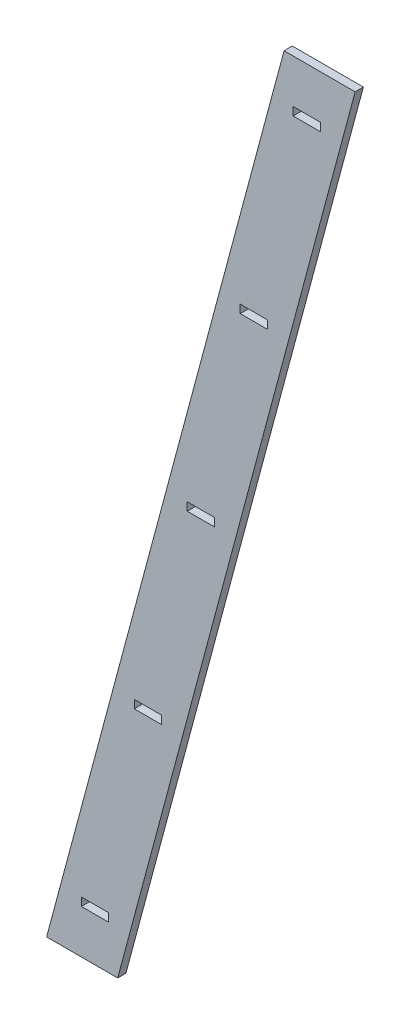
SolidWorks part; units mm, degrees
ref_plane "Alzado" through (0, 0, 0) normal (0, 0, 1) x (1, 0, 0)
ref_plane "Planta" through (0, 0, 0) normal (0, 1, 0) x (1, 0, 0)
ref_plane "Vista lateral" through (0, 0, 0) normal (1, 0, 0) x (0, 0, -1)
sketch "Croquis1" plane through (0, 0, 0) normal (0, 0, 1) x (1, 0, 0)
  line L0 (273.3305, 777.5) -> (-152.0388, -810)
  line L1 (273.3305, 777.5) -> (152.0388, 810) construction
  line L2 (-152.0388, -810) -> (-273.3305, -777.5) construction
  line L3 (152.0388, 810) -> (-273.3305, -777.5)
  line L4 (273.3305, 777.5) -> (-273.3305, -777.5) construction
  line L5 (-152.0388, -810) -> (152.0388, 810) construction
  line L6 (-152.0388, -810) -> (74.6817, -810) construction
  line L7 (-273.3305, -777.5) -> (-282.0388, -810)
  line L8 (-282.0388, -810) -> (-152.0388, -810)
  line L10 (282.0388, 810) -> (152.0388, 810)
  line L11 (273.3305, 777.5) -> (282.0388, 810)
  line L12 (0, 0) -> (-141.1281, 0) construction
  line L13 (-25, -7.5) -> (25, -7.5)
  line L14 (-25, -7.5) -> (-25, 7.5)
  line L15 (-25, 7.5) -> (25, 7.5)
  line L16 (25, -7.5) -> (25, 7.5)
  line L17 (-25, -7.5) -> (25, 7.5) construction
  line L18 (-25, 7.5) -> (25, -7.5) construction
  line L19 (-217.0388, -810) -> (217.0388, 810) construction
  line L21 (-218.5933, -730) -> (-168.5933, -730)
  line L22 (-218.5933, -730) -> (-218.5933, -715)
  line L23 (-218.5933, -715) -> (-168.5933, -715)
  line L24 (-168.5933, -730) -> (-168.5933, -715)
  line L25 (-218.5933, -730) -> (-168.5933, -715) construction
  line L26 (-218.5933, -715) -> (-168.5933, -730) construction
  line L27 (-121.7966, -368.75) -> (-71.7966, -368.75)
  line L28 (-121.7966, -368.75) -> (-121.7966, -353.75)
  line L29 (-121.7966, -353.75) -> (-71.7966, -353.75)
  line L30 (-71.7966, -368.75) -> (-71.7966, -353.75)
  line L31 (-121.7966, -368.75) -> (-71.7966, -353.75) construction
  line L32 (-121.7966, -353.75) -> (-71.7966, -368.75) construction
  line L33 (71.7966, 353.75) -> (121.7966, 353.75)
  line L34 (71.7966, 353.75) -> (71.7966, 368.75)
  line L35 (71.7966, 368.75) -> (121.7966, 368.75)
  line L36 (121.7966, 353.75) -> (121.7966, 368.75)
  line L37 (71.7966, 353.75) -> (121.7966, 368.75) construction
  line L38 (71.7966, 368.75) -> (121.7966, 353.75) construction
  line L39 (168.5933, 715) -> (218.5933, 715)
  line L40 (168.5933, 715) -> (168.5933, 730)
  line L41 (168.5933, 730) -> (218.5933, 730)
  line L42 (218.5933, 715) -> (218.5933, 730)
  line L43 (168.5933, 715) -> (218.5933, 730) construction
  line L44 (168.5933, 730) -> (218.5933, 715) construction
  point P1 (0, 0)
  point P11 (0, 0)
  point P18 (-193.5933, -722.5)
  point P23 (-96.7966, -361.25)
  point P30 (96.7966, 361.25)
  point P35 (193.5933, 722.5)
  dimension "D1" = 75
  dimension "D2" = 1620
  dimension "D3" = 130
  dimension "D4" = 50
  dimension "D5" = 15
  dimension "D6" = 80
  dimension "D7" = 50
  dimension "D8" = 15
  dimension "D9" = 50
  dimension "D10" = 15
  dimension "D11" = 361.25
  dimension "D12" = 361.25
  dimension "D13" = 80
  dimension "D14" = 15
  dimension "D15" = 50
  dimension "D16" = 15
  dimension "D17" = 50
  dimension "D18" = 141.1281
extrude "Saliente-Extruir1" add sketch "Croquis1" along normal blind 15
